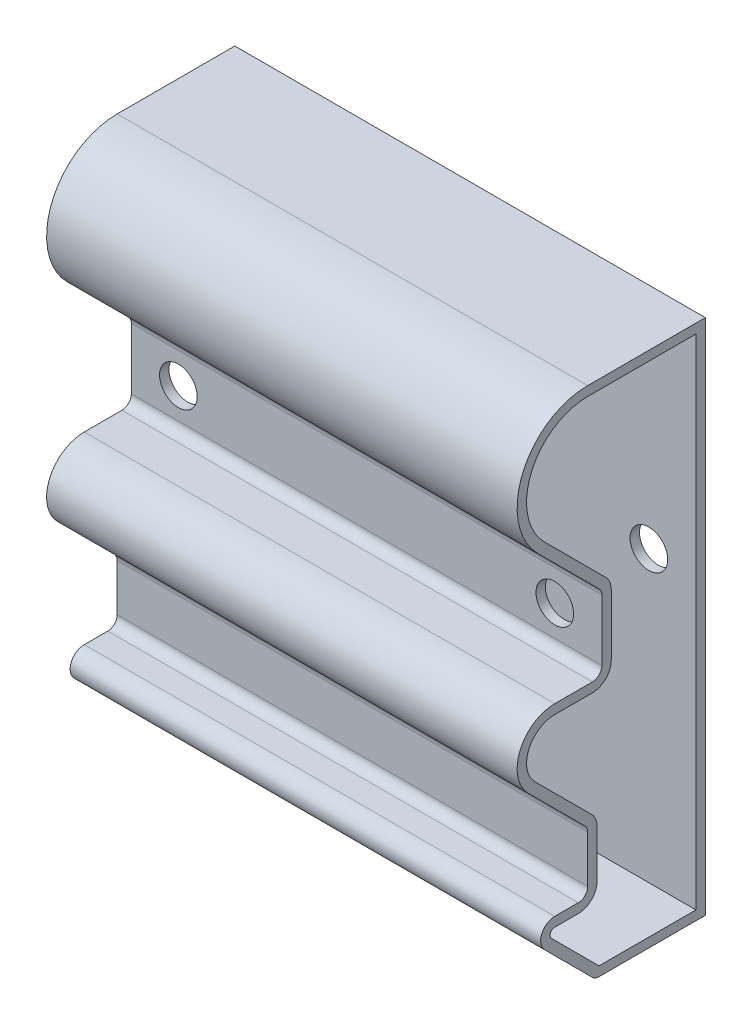
SolidWorks part; units mm, degrees
ref_plane "Front" through (0, 0, 0) normal (0, 0, 1) x (1, 0, 0)
ref_plane "Top" through (0, 0, 0) normal (0, 1, 0) x (1, 0, 0)
ref_plane "Right" through (0, 0, 0) normal (1, 0, 0) x (0, 0, -1)
sketch "Croquis1" plane through (0, 0, 0) normal (1, 0, 0) x (0, 0, -1)
  line L1 (0, 0) -> (-22.598, 0)
  line L2 (0, 0) -> (0, 110)
  line L3 (0, 110) -> (-25, 110)
  line L5 (-32, 54.9584) -> (-24, 54.9584)
  line L10 (-22, 69.9584) -> (-22, 56.9584)
  line L14 (-25, 17.8162) -> (-25, 27.8162)
  line L16 (-37.6569, 41.3015) -> (-25.5858, 29.2304)
  line L17 (-32, 15.8162) -> (-27, 15.8162)
  line L18 (-35.6066, 84.3934) -> (-22.5858, 71.3726)
  line L19 (-34.1213, 10.6949) -> (-24.0122, 0.5858)
  arc A2 (-25, 110) -> (-35.6066, 84.3934) centre (-25, 95) ccw
  arc A3 (-32, 15.8162) -> (-34.1213, 10.6949) centre (-32, 12.8162) ccw
  arc A6 (-32, 54.9584) -> (-37.6569, 41.3015) centre (-32, 46.9584) ccw
  arc A8 (-22.5858, 71.3726) -> (-22, 69.9584) centre (-24, 69.9584) cw
  arc A9 (-22, 56.9584) -> (-24, 54.9584) centre (-24, 56.9584) cw
  arc A10 (-25.5858, 29.2304) -> (-25, 27.8162) centre (-27, 27.8162) cw
  arc A11 (-25, 17.8162) -> (-27, 15.8162) centre (-27, 17.8162) cw
  arc A12 (-22.598, 0) -> (-24.0122, 0.5858) centre (-22.598, 2) cw
  point P0 (0, 0)
  point P11 (-22, 54.9584)
  dimension "D1" = 2
  dimension "D2" = 15
  dimension "D8" = 8
  dimension "D9" = 45
  dimension "D12" = 2
  dimension "D7" = 2
  dimension "D10" = 2
  dimension "D11" = 2
  dimension "D16" = 40
  dimension "D19" = 110
  dimension "D14" = 10
  dimension "D6" = 3
  dimension "D3" = 40
  dimension "D4" = 45
  dimension "D5" = 18
  dimension "D13" = 45
  dimension "D15" = 15
  dimension "D17" = 15
  dimension "D18" = 12
extrude "Saliente-Extruir1" add sketch "Croquis1" along normal blind 100
sketch "Croquis2" plane through (0, 0, 22) normal (0, 0, 1) x (1, 0, 0)
  line L0 (0, 63.4584) -> (100, 63.4584) construction
  line L1 (0, 69.9584) -> (0, 56.9584) construction
  line L2 (100, 69.9584) -> (100, 56.9584) construction
  circle A0 centre (10, 63.4584) radius 4
  circle A1 centre (90, 63.4584) radius 4
  dimension "D1" = 8
  dimension "D2" = 8
  dimension "D3" = 10
  dimension "D4" = 10
extrude "Cortar-Extruir1" cut sketch "Croquis2" against normal through all
sketch "Croquis3" plane through (100, 0, 0) normal (1, 0, 0) x (0, 0, -1)
  line L20 (-24, 52.9584) -> (-32, 52.9584)
  line L21 (-36.2426, 42.7157) -> (-24.1716, 30.6447)
  line L22 (-23, 27.8162) -> (-23, 17.8162)
  line L23 (-27, 13.8162) -> (-32, 13.8162)
  line L24 (-32.7071, 12.1091) -> (-22.598, 2)
  line L25 (-22.598, 2) -> (-2, 2)
  line L26 (-2, 2) -> (-2, 108)
  line L27 (-2, 108) -> (-25, 108)
  line L28 (-34.1924, 85.8076) -> (-21.1716, 72.7868)
  line L29 (-20, 69.9584) -> (-20, 56.9584)
  line L30 (-24, 52.9584) -> (-32, 52.9584)
  line L31 (-36.2426, 42.7157) -> (-24.1716, 30.6447)
  line L32 (-23, 27.8162) -> (-23, 17.8162)
  line L33 (-27, 13.8162) -> (-32, 13.8162)
  line L34 (-32.7071, 12.1091) -> (-22.598, 2)
  line L35 (-22.598, 2) -> (-2, 2)
  line L36 (-2, 2) -> (-2, 108)
  line L37 (-2, 108) -> (-25, 108)
  line L38 (-34.1924, 85.8076) -> (-21.1716, 72.7868)
  line L39 (-20, 69.9584) -> (-20, 56.9584)
  arc A16 (-24, 52.9584) -> (-20, 56.9584) centre (-24, 56.9584) ccw
  arc A17 (-32, 52.9584) -> (-36.2426, 42.7157) centre (-32, 46.9584) ccw
  arc A18 (-23, 27.8162) -> (-24.1716, 30.6447) centre (-27, 27.8162) ccw
  arc A19 (-27, 13.8162) -> (-23, 17.8162) centre (-27, 17.8162) ccw
  arc A20 (-32, 13.8162) -> (-32.7071, 12.1091) centre (-32, 12.8162) ccw
  arc A21 (-25, 108) -> (-34.1924, 85.8076) centre (-25, 95) ccw
  arc A22 (-20, 69.9584) -> (-21.1716, 72.7868) centre (-24, 69.9584) ccw
  arc A23 (-24, 52.9584) -> (-20, 56.9584) centre (-24, 56.9584) ccw
  arc A24 (-32, 52.9584) -> (-36.2426, 42.7157) centre (-32, 46.9584) ccw
  arc A25 (-23, 27.8162) -> (-24.1716, 30.6447) centre (-27, 27.8162) ccw
  arc A26 (-27, 13.8162) -> (-23, 17.8162) centre (-27, 17.8162) ccw
  arc A27 (-32, 13.8162) -> (-32.7071, 12.1091) centre (-32, 12.8162) ccw
  arc A28 (-25, 108) -> (-34.1924, 85.8076) centre (-25, 95) ccw
  arc A29 (-20, 69.9584) -> (-21.1716, 72.7868) centre (-24, 69.9584) ccw
  dimension "D1" = 2
extrude "Cortar-Extruir3" cut sketch "Croquis3" against normal through all
